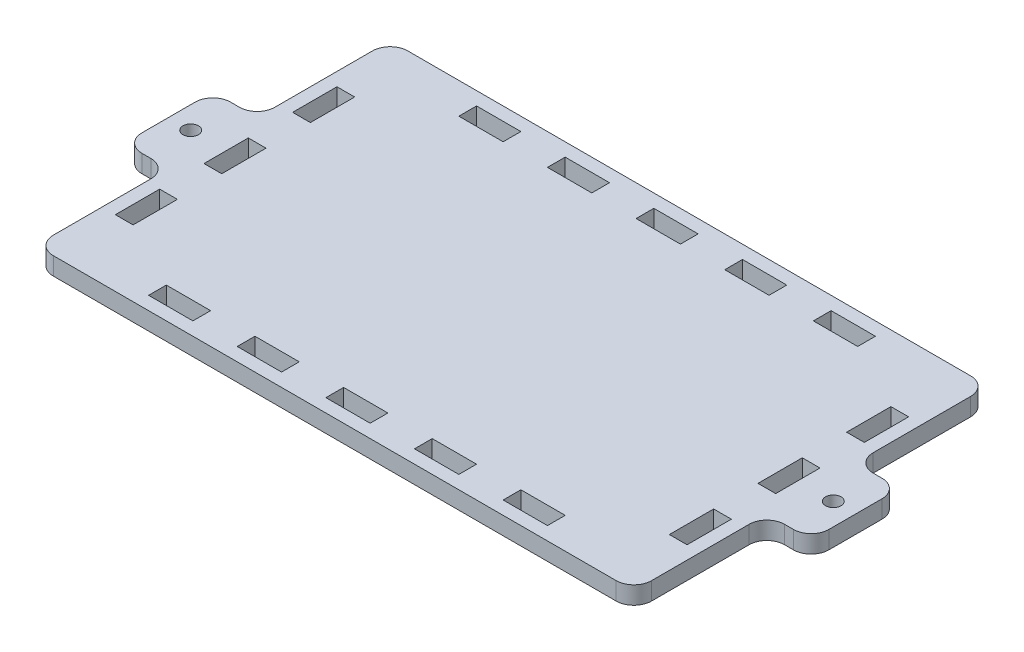
SolidWorks part; units mm, degrees
material "Maple"
ref_plane "Front Plane" through (0, 0, 0) normal (0, 0, 1) x (1, 0, 0)
ref_plane "Top Plane" through (0, 0, 0) normal (0, 1, 0) x (1, 0, 0)
ref_plane "Right Plane" through (0, 0, 0) normal (1, 0, 0) x (0, 0, -1)
sketch "Sketch1" plane through (0, 0, 0) normal (0, 1, 0) x (1, 0, 0)
  line L1 (0, 0) -> (129, 0)
  line L2 (0, 0) -> (0, -74)
  line L3 (0, -74) -> (129, -74)
  line L4 (129, 0) -> (129, -74)
  dimension "D1" = 129
  dimension "D2" = 74
extrude "Boss-Extrude1" add sketch "Sketch1" along normal blind 4
sketch "Sketch4" plane through (0, 4, 0) normal (0, 1, 0) x (1, 0, 0)
  line L0 (129, -74) -> (129, 0) construction
  line L1 (129, -62) -> (125, -62)
  line L2 (129, -62) -> (129, -52)
  line L3 (129, -52) -> (125, -52)
  line L4 (125, -62) -> (125, -52)
  line L5 (129, -42) -> (125, -42)
  line L6 (129, -42) -> (129, -32)
  line L7 (129, -32) -> (125, -32)
  line L8 (125, -42) -> (125, -32)
  line L9 (0, 0) -> (0, -74) construction
  line L10 (129, -22) -> (125, -22)
  line L11 (129, -22) -> (129, -12)
  line L12 (129, -12) -> (125, -12)
  line L13 (125, -22) -> (125, -12)
  line L14 (0, -62) -> (4, -62)
  line L15 (0, -62) -> (0, -52)
  line L16 (0, -52) -> (4, -52)
  line L17 (4, -62) -> (4, -52)
  line L18 (0, -42) -> (4, -42)
  line L19 (0, -42) -> (0, -32)
  line L20 (0, -32) -> (4, -32)
  line L21 (4, -42) -> (4, -32)
  line L22 (129, 0) -> (0, 0) construction
  line L23 (0, -22) -> (4, -22)
  line L24 (0, -22) -> (0, -12)
  line L25 (0, -12) -> (4, -12)
  line L26 (4, -22) -> (4, -12)
  line L27 (109.5, -4) -> (99.5, -4)
  line L28 (109.5, -4) -> (109.5, 0)
  line L29 (109.5, 0) -> (99.5, 0)
  line L30 (99.5, -4) -> (99.5, 0)
  line L31 (0, -74) -> (129, -74) construction
  line L32 (89.5, -4) -> (79.5, -4)
  line L33 (89.5, -4) -> (89.5, 0)
  line L34 (89.5, 0) -> (79.5, 0)
  line L35 (79.5, -4) -> (79.5, 0)
  line L36 (69.5, -4) -> (59.5, -4)
  line L37 (69.5, -4) -> (69.5, 0)
  line L38 (69.5, 0) -> (59.5, 0)
  line L39 (59.5, -4) -> (59.5, 0)
  line L40 (49.5, -4) -> (39.5, -4)
  line L41 (49.5, -4) -> (49.5, 0)
  line L42 (49.5, 0) -> (39.5, 0)
  line L43 (39.5, -4) -> (39.5, 0)
  line L44 (29.5, -4) -> (19.5, -4)
  line L45 (29.5, -4) -> (29.5, 0)
  line L46 (29.5, 0) -> (19.5, 0)
  line L47 (19.5, -4) -> (19.5, 0)
  line L48 (109.5, -74) -> (99.5, -74)
  line L49 (109.5, -74) -> (109.5, -70)
  line L50 (109.5, -70) -> (99.5, -70)
  line L51 (99.5, -74) -> (99.5, -70)
  line L53 (89.5, -74) -> (79.5, -74)
  line L54 (89.5, -74) -> (89.5, -70)
  line L55 (89.5, -70) -> (79.5, -70)
  line L56 (79.5, -74) -> (79.5, -70)
  line L57 (69.5, -74) -> (59.5, -74)
  line L58 (69.5, -74) -> (69.5, -70)
  line L59 (69.5, -70) -> (59.5, -70)
  line L60 (59.5, -74) -> (59.5, -70)
  line L61 (49.5, -74) -> (39.5, -74)
  line L62 (49.5, -74) -> (49.5, -70)
  line L63 (49.5, -70) -> (39.5, -70)
  line L64 (39.5, -74) -> (39.5, -70)
  line L65 (29.5, -74) -> (19.5, -74)
  line L66 (29.5, -74) -> (29.5, -70)
  line L67 (29.5, -70) -> (19.5, -70)
  line L68 (19.5, -74) -> (19.5, -70)
extrude "Cut-Extrude3" cut sketch "Sketch4" against normal through all
sketch "Sketch5" plane through (0, 4, 0) normal (0, 1, 0) x (1, 0, 0)
  line L0 (4, -37) -> (125, -37) construction
  line L1 (4, -42) -> (4, -32) construction
  line L2 (125, -32) -> (125, -42) construction
  line L3 (19.5, 0) -> (0, 0) construction
  line L4 (0, 0) -> (129, 0)
  line L5 (0, 0) -> (0, -74)
  line L6 (0, -74) -> (129, -74)
  line L7 (129, 0) -> (129, -74)
  line L8 (0, 0) -> (129, -74) construction
  line L9 (0, -74) -> (129, 0) construction
  line L10 (-3, 3) -> (132, 3)
  line L11 (-3, 3) -> (-3, -77)
  line L12 (-3, -77) -> (132, -77)
  line L13 (132, 3) -> (132, -77)
  line L14 (-3, 3) -> (132, -77) construction
  line L15 (-3, -77) -> (132, 3) construction
  line L16 (0, -42) -> (0, -52) construction
  point P6 (64.5, -37)
  point P11 (64.5, -37)
  dimension "D1" = 3
  dimension "D2" = 3
extrude "Boss-Extrude2" add sketch "Sketch5" against normal through all
sketch "Sketch6" plane through (0, 0, 0) normal (0, -1, 0) x (1, 0, 0)
  line L0 (132, 37) -> (-3, 37) construction
  line L1 (132, 77) -> (132, -3) construction
  line L2 (-3, -3) -> (-3, 77) construction
  line L4 (142, 27) -> (132, 27)
  line L5 (142, 27) -> (142, 47)
  line L6 (142, 47) -> (132, 47)
  line L7 (132, 27) -> (132, 47)
  line L8 (142, 27) -> (132, 47) construction
  line L9 (142, 47) -> (132, 27) construction
  line L10 (-3, 27) -> (-13, 27)
  line L11 (-3, 27) -> (-3, 47)
  line L12 (-3, 47) -> (-13, 47)
  line L13 (-13, 27) -> (-13, 47)
  line L14 (-3, 27) -> (-13, 47) construction
  line L15 (-3, 47) -> (-13, 27) construction
  circle A0 centre (137, 37) radius 1.75
  circle A1 centre (-8, 37) radius 1.75
  point P6 (137, 37)
  point P12 (-8, 37)
  dimension "D3" = 3.5
  dimension "D1" = 10
  dimension "D2" = 20
extrude "Boss-Extrude3" add sketch "Sketch6" against normal through all
fillet "Fillet1" radius 4 12 edges at (-3, 2, -3) (-3, 2, 77) (132, 2, 77) (132, 2, -3) (-13, 2, 27) (-3, 2, 27) (-13, 2, 47) (-3, 2, 47) (132, 2, 47) (142, 2, 47) (132, 2, 27) (142, 2, 27)
equation "\"D1@Sketch5\"=\"D2@Sketch5\""
